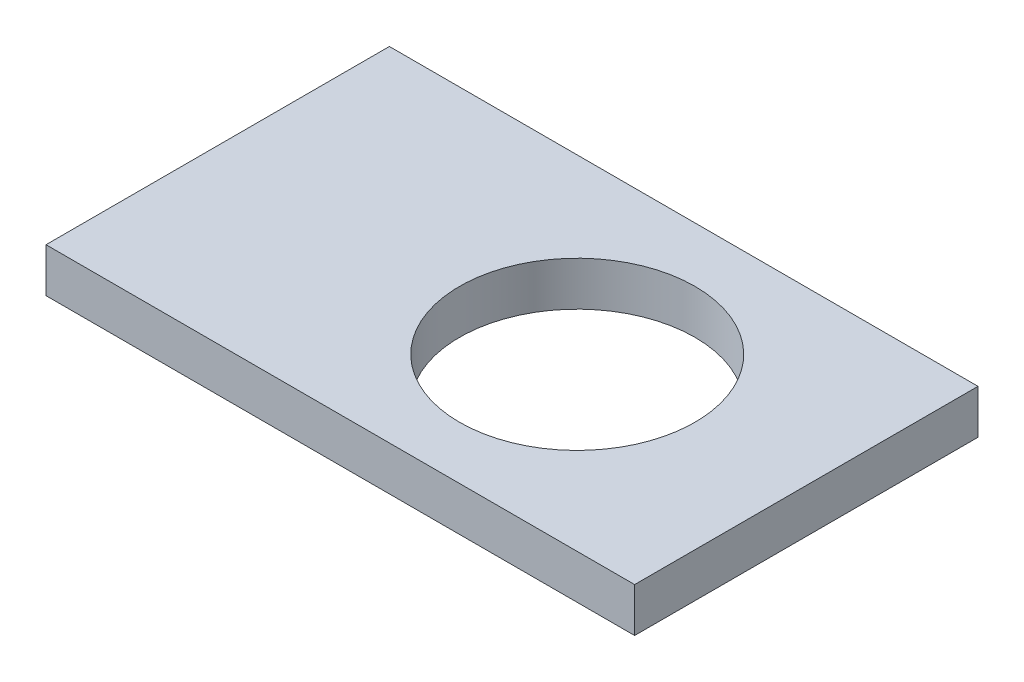
SolidWorks part; units mm, degrees
ref_plane "Front Plane" through (0, 0, 0) normal (0, 0, 1) x (1, 0, 0)
ref_plane "Top Plane" through (0, 0, 0) normal (0, 1, 0) x (1, 0, 0)
ref_plane "Right Plane" through (0, 0, 0) normal (1, 0, 0) x (0, 0, -1)
sketch "Sketch1" plane through (0, 0, 0) normal (0, 1, 0) x (1, 0, 0)
  line L1 (0, 0) -> (80, 0)
  line L2 (0, 0) -> (0, 60)
  line L3 (0, 60) -> (80, 60)
  line L4 (80, 0) -> (80, 60)
  circle A0 centre (49, 23.2) radius 16
  dimension "D3" = 32
  dimension "D5" = 49
  dimension "D1" = 80
  dimension "D2" = 60
  dimension "D4" = 36.8
extrude "Boss-Extrude1" add sketch "Sketch1" along normal blind 6
scale "Scale1" scale about centroid uniform scaling yes scale factor 7.5
sketch "Sketch2" plane through (0, 25.5, 0) normal (0, 1, 0) x (1, 0, 0)
  line L6 (-313.3739, 260.3903) -> (428.5681, 260.3903)
  line L7 (-313.3739, 260.3903) -> (-313.3739, 146.1036)
  line L8 (-313.3739, 146.1036) -> (428.5681, 146.1036)
  line L9 (428.5681, 260.3903) -> (428.5681, 146.1036)
  dimension "D1" = 100
extrude "Cut-Extrude1" cut sketch "Sketch2" against normal through all
